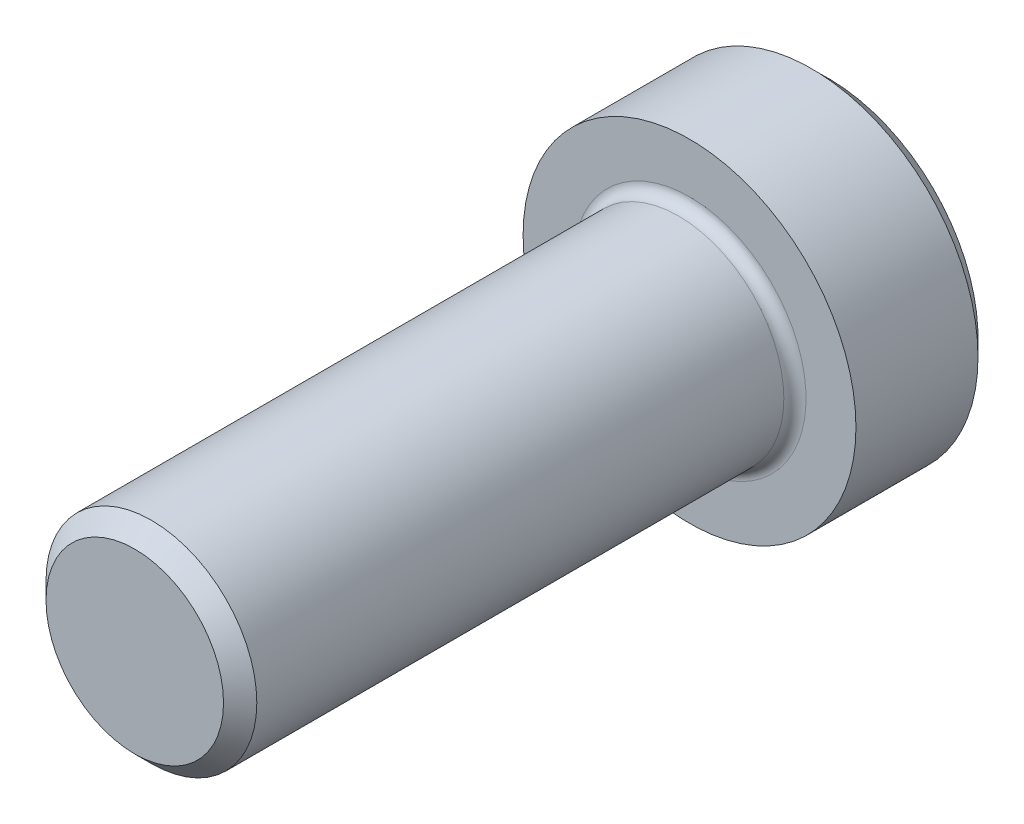
SolidWorks part; units mm, degrees
ref_plane "Front Plane" through (0, 0, 0) normal (0, 0, 1) x (1, 0, 0)
ref_plane "Top Plane" through (0, 0, 0) normal (0, 1, 0) x (1, 0, 0)
ref_plane "Right Plane" through (0, 0, 0) normal (1, 0, 0) x (0, 0, -1)
sketch "Sketch1" plane through (0, 0, 0) normal (0, 0, 1) x (1, 0, 0)
  circle A0 centre (0, 0) radius 0.19
  dimension "D1" = 0.38
extrude "Boss-Extrude1" add sketch "Sketch1" along normal blind 1
sketch "Sketch2" plane through (0, 0, 0) normal (0, 0, -1) x (-1, 0, 0)
  circle A0 centre (0, 0) radius 0.3
  dimension "D1" = 0.6
extrude "Boss-Extrude2" add sketch "Sketch2" along normal blind 0.25
chamfer "Chamfer1" distance 0.03 angle 45 2 edges at (-0.3, 0, -0.25) (0.19, 0, 1)
fillet "Fillet1" radius 0.02 1 edges at (0.19, 0, 0)
sketch "Sketch3" plane through (0, 0, -0.25) normal (0, 0, -1) x (-1, 0, 0)
  line L1 (0.2021, 0) -> (0.101, 0.175)
  line L2 (0.101, 0.175) -> (-0.101, 0.175)
  line L3 (-0.101, 0.175) -> (-0.2021, 0)
  line L4 (-0.2021, 0) -> (-0.101, -0.175)
  line L5 (-0.101, -0.175) -> (0.101, -0.175)
  line L6 (0.101, -0.175) -> (0.2021, 0)
  circle A0 centre (0, 0) radius 0.175 construction
  circle A1 centre (0, 0) radius 0.27 construction
  dimension "D1" = 0.35
  dimension "D2" = 0.2021
extrude "Cut-Extrude1" cut sketch "Sketch3" against normal blind 0.15
sketch "Sketch4" plane through (0, 0, -0.1) normal (0, 0, -1) x (-1, 0, 0)
  line L6 (0.101, -0.175) -> (0.2021, 0)
  line L7 (0.2021, 0) -> (0.101, 0.175)
  line L8 (0.101, 0.175) -> (-0.101, 0.175)
  line L9 (-0.101, 0.175) -> (-0.2021, 0)
  line L10 (-0.2021, 0) -> (-0.101, -0.175)
  line L11 (-0.101, -0.175) -> (0.101, -0.175)
  line L12 (0.101, -0.175) -> (0.2021, 0)
  line L13 (0.2021, 0) -> (0.101, 0.175)
  line L14 (0.101, 0.175) -> (-0.101, 0.175)
  line L15 (-0.101, 0.175) -> (-0.2021, 0)
  line L16 (-0.2021, 0) -> (-0.101, -0.175)
  line L17 (-0.101, -0.175) -> (0.101, -0.175)
  circle A0 centre (0, 0) radius 0.175
  dimension "D1" = 0
extrude "Cut-Extrude2" cut sketch "Sketch4" against normal blind 0.1 draft 60 contours A0 L16
